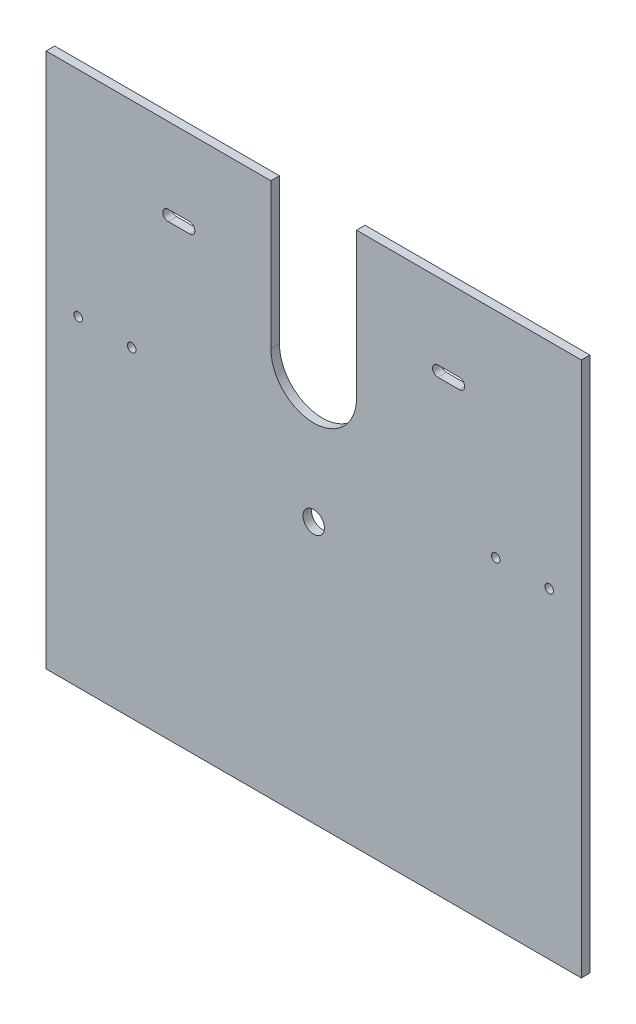
SolidWorks part; units mm, degrees
ref_plane "Front Plane" through (0, 0, 0) normal (0, 0, 1) x (1, 0, 0)
ref_plane "Top Plane" through (0, 0, 0) normal (0, 1, 0) x (1, 0, 0)
ref_plane "Right Plane" through (0, 0, 0) normal (1, 0, 0) x (0, 0, -1)
sketch "Sketch1" plane through (0, 0, 0) normal (0, 0, 1) x (1, 0, 0)
  line L1 (125, -100) -> (-125, -100)
  line L2 (125, -100) -> (125, 100)
  line L3 (125, 100) -> (-125, 100)
  line L4 (-125, -100) -> (-125, 100)
  line L5 (125, -100) -> (-125, 100) construction
  line L6 (125, 100) -> (-125, -100) construction
  point P0 (0, 0)
  dimension "D1" = 200
  dimension "D2" = 250
extrude "Boss-Extrude1" add sketch "Sketch1" along normal blind 4
sketch "Sketch2" plane through (0, 0, 4) normal (0, 0, 1) x (1, 0, 0)
  line L0 (-125, 0) -> (125, 0) construction
  line L1 (-125, 100) -> (-125, -100) construction
  line L2 (125, -100) -> (125, 100) construction
  circle A0 centre (-110, 0) radius 2
  circle A1 centre (-85, 0) radius 2
  circle A2 centre (110, 0) radius 2
  circle A3 centre (85, 0) radius 2
  dimension "D3" = 4
  dimension "D1" = 25
  dimension "25" = 25
  dimension "D2" = 15
  dimension "15" = 15
extrude "Cut-Extrude1" cut sketch "Sketch2" against normal blind 4
sketch "Sketch3" plane through (0, 0, 4) normal (0, 0, 1) x (1, 0, 0)
  line L0 (125, 100) -> (-125, 100) construction
  line L1 (0, -28) -> (0, 100) construction
  line L3 (20, 32) -> (20, 100)
  line L5 (-20, 32) -> (-20, 100)
  line L6 (-20, 100) -> (20, 100)
  line L7 (-68, 64.5) -> (-58, 64.5)
  line L8 (-68, 59.5) -> (-58, 59.5)
  line L9 (58, 59.5) -> (68, 59.5)
  line L11 (58, 64.5) -> (68, 64.5)
  circle A0 centre (0, -28) radius 5
  arc A7 (-68, 64.5) -> (-68, 59.5) centre (-68, 62) ccw
  arc A8 (68, 59.5) -> (68, 64.5) centre (68, 62) ccw
  arc A9 (-20, 32) -> (20, 32) centre (0, 32) ccw
  arc A10 (-58, 59.5) -> (-58, 64.5) centre (-58, 62) ccw
  arc A11 (58, 64.5) -> (58, 59.5) centre (58, 62) ccw
  point P12 (0, 0)
  point P16 (40, 32)
  point P18 (0, 61.835)
  dimension "D1" = 10
  dimension "D4" = 40
  dimension "D6" = 5
  dimension "D3" = 40
  dimension "D11" = 5
  dimension "D12" = 5
  dimension "D2" = 28
  dimension "D5" = 90
  dimension "D7" = 68
  dimension "D8" = 68
  dimension "D9" = 10
  dimension "D10" = 10
extrude "Cut-Extrude2" cut sketch "Sketch3" against normal blind 4
sketch "Sketch8" plane through (0, -100, 0) normal (0, -1, 0) x (1, 0, 0)
  line L0 (-125, 4) -> (125, 4) construction
  line L1 (-125, 4) -> (125, 4)
  line L2 (-125, 4) -> (-125, 0) construction
  line L3 (-125, 4) -> (-125, 0)
  line L4 (-125, 0) -> (125, 0) construction
  line L5 (-125, 0) -> (125, 0)
  line L6 (125, 4) -> (125, 0) construction
  line L7 (125, 4) -> (125, 0)
extrude "Boss-Extrude2" add sketch "Sketch8" along normal blind 50
